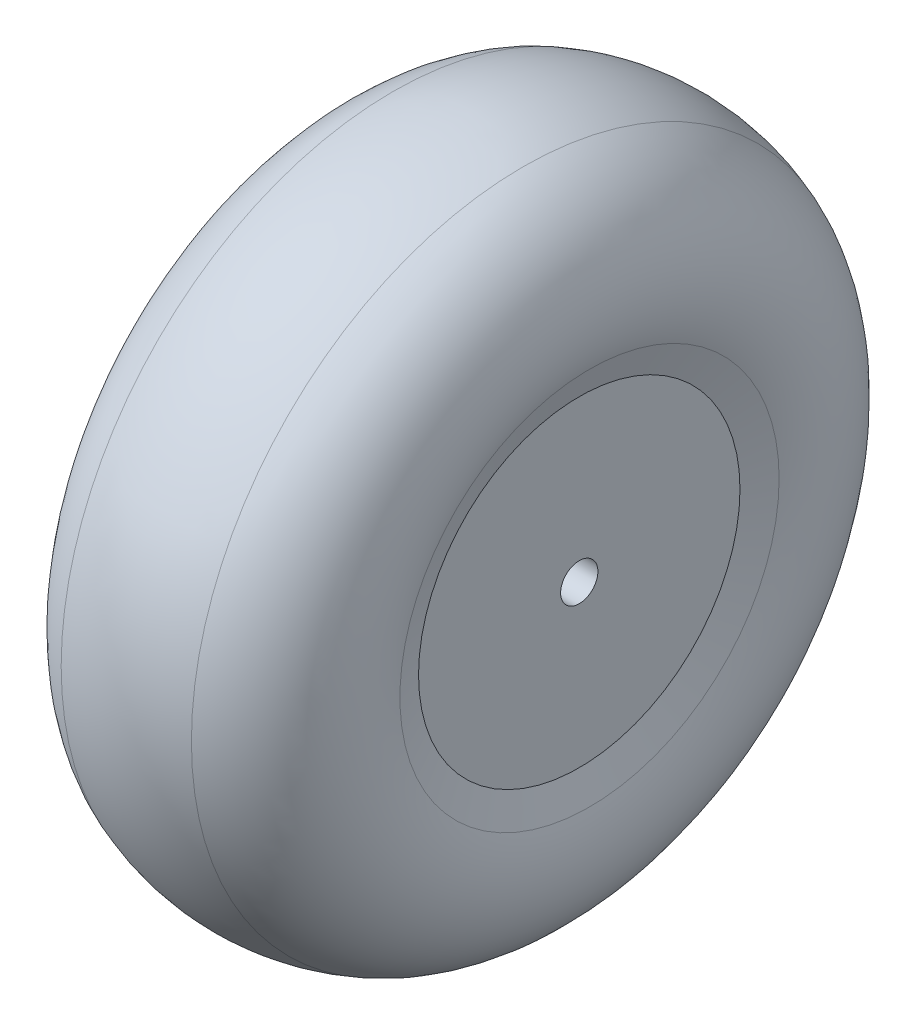
SolidWorks part; units mm, degrees
ref_plane "Front Plane" through (0, 0, 0) normal (0, 0, 1) x (1, 0, 0)
ref_plane "Top Plane" through (0, 0, 0) normal (0, 1, 0) x (1, 0, 0)
ref_plane "Right Plane" through (0, 0, 0) normal (1, 0, 0) x (0, 0, -1)
sketch "Sketch1" plane through (0, 0, 0) normal (1, 0, 0) x (0, 0, -1)
  circle A0 centre (0, 0) radius 17.25
  dimension "D1" = 34.5
extrude "Boss-Extrude1" add sketch "Sketch1" along normal blind 26
sketch "Sketch2" plane through (0, 0, 0) normal (0, 0, 1) x (1, 0, 0)
  line L0 (0, 17.25) -> (13, 37.75) construction
  line L1 (13, 17.25) -> (13, 37.75) construction
  line L2 (26, 17.25) -> (0, 17.25) construction
  line L3 (13, 37.75) -> (26, 17.25) construction
  line L4 (-4.6227, 30.25) -> (0, 17.25)
  line L5 (30.6227, 30.25) -> (26, 17.25)
  line L6 (0, 17.25) -> (26, 17.25)
  line L7 (0, 0) -> (26, 0) construction
  line L8 (0, 17.25) -> (0, -17.25) construction
  line L9 (26, -17.25) -> (26, 17.25) construction
  arc A0 (13, 37.75) -> (-4.6227, 30.25) centre (26, -17.25) ccw
  arc A1 (13, 37.75) -> (30.6227, 30.25) centre (0, -17.25) cw
  dimension "D1" = 20.5
  dimension "D2" = 13
revolve "Revolve1" add sketch "Sketch2" angle 360 about L7
fillet "Fillet1" radius 20 1 edges at (13, 0, 37.75)
fillet "Fillet2" radius 12 2 edges at (-4.6227, 0, 30.25) (30.6227, 0, 30.25)
sketch "Sketch3" plane through (0, 0, 0) normal (-1, 0, 0) x (0, 0, 1)
  circle A0 centre (0, 0) radius 2
  dimension "D1" = 4
extrude "Cut-Extrude1" cut sketch "Sketch3" against normal through all both
